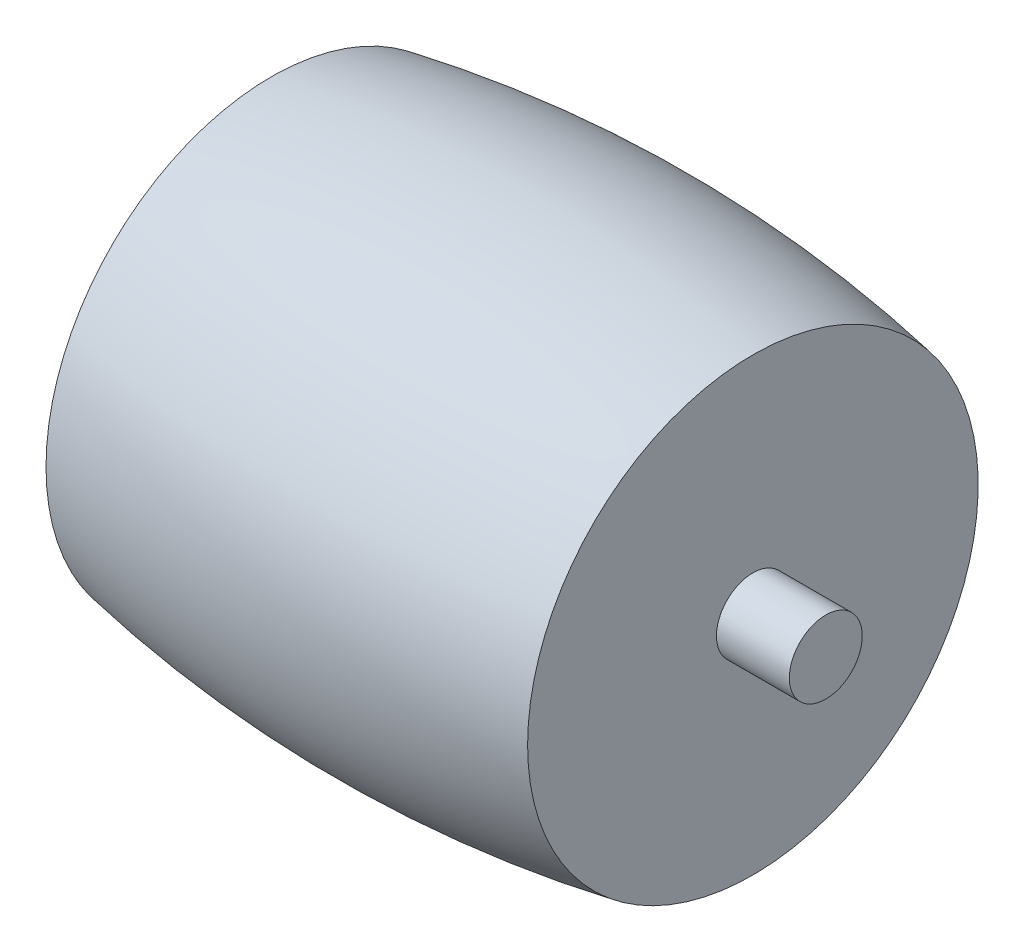
SolidWorks part; units mm, degrees
material "POLYURETHANE (11671)"
ref_plane "Front Plane" through (0, 0, 0) normal (0, 0, 1) x (1, 0, 0)
ref_plane "Top Plane" through (0, 0, 0) normal (0, 1, 0) x (1, 0, 0)
ref_plane "Right Plane" through (0, 0, 0) normal (1, 0, 0) x (0, 0, -1)
sketch "Sketch1" plane through (0, 0, 0) normal (0, 0, 1) x (1, 0, 0)
  line L1 (0, 51) -> (0, 41.5) construction
  line L2 (9.25, 50.1541) -> (9.25, 42.9)
  line L3 (-9.25, 41.5) -> (-12.05, 41.5)
  line L4 (-9.25, 41.5) -> (9.25, 41.5)
  line L7 (-12.05, 42.9) -> (-12.05, 41.5)
  line L8 (9.25, 42.9) -> (12.05, 42.9)
  line L9 (-9.25, 42.9) -> (-12.05, 42.9)
  line L10 (9.25, 41.5) -> (12.05, 41.5)
  line L11 (12.05, 42.9) -> (12.05, 41.5)
  line L12 (-9.25, 50.1541) -> (-9.25, 42.9)
  arc A0 (9.25, 50.1541) -> (-9.25, 50.1541) centre (0, 0) ccw
  dimension "D1" = 102
  dimension "D2" = 18.5
  dimension "D3" = 9.5
  dimension "D4" = 2.8
  dimension "D5" = 1.4
revolve "Revolve1" add sketch "Sketch1" angle 360 about L4
